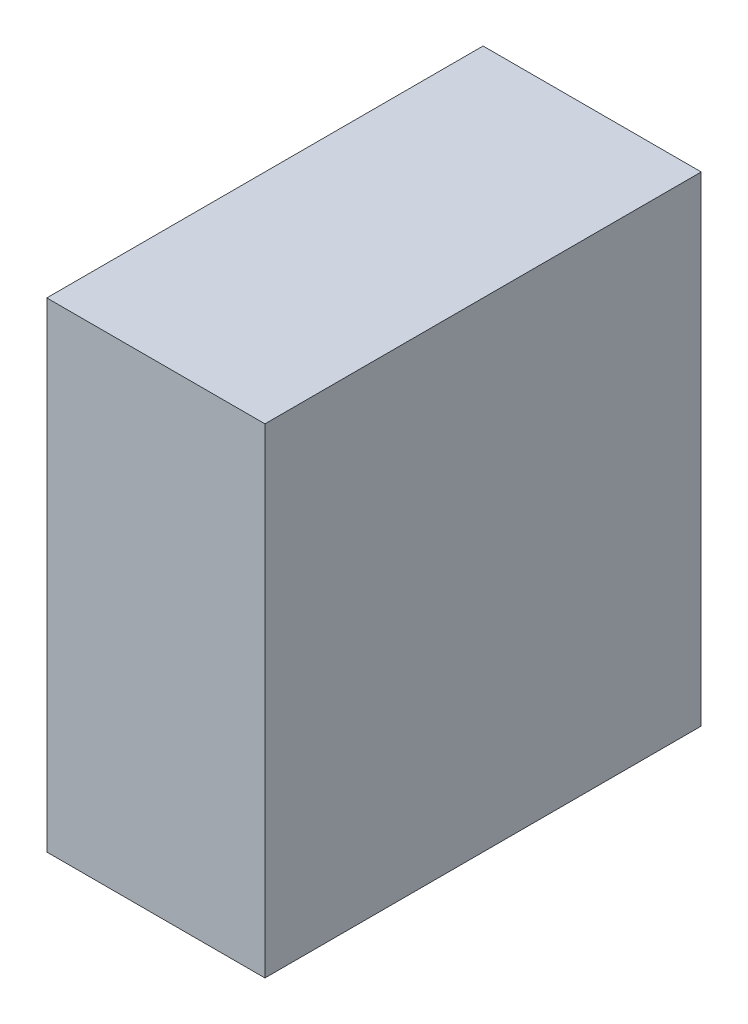
SolidWorks part; units mm, degrees
ref_plane "Front Plane" through (0, 0, 0) normal (0, 0, 1) x (1, 0, 0)
ref_plane "Top Plane" through (0, 0, 0) normal (0, 1, 0) x (1, 0, 0)
ref_plane "Right Plane" through (0, 0, 0) normal (1, 0, 0) x (0, 0, -1)
sketch "Sketch1" plane through (0, 0, 0) normal (0, 1, 0) x (1, 0, 0)
  line L1 (0, 0) -> (5, 0)
  line L2 (0, 0) -> (0, -10)
  line L3 (0, -10) -> (5, -10)
  line L4 (5, 0) -> (5, -10)
  dimension "D1" = 5
  dimension "D2" = 10
extrude "Boss-Extrude1" add sketch "Sketch1" along normal blind 11
